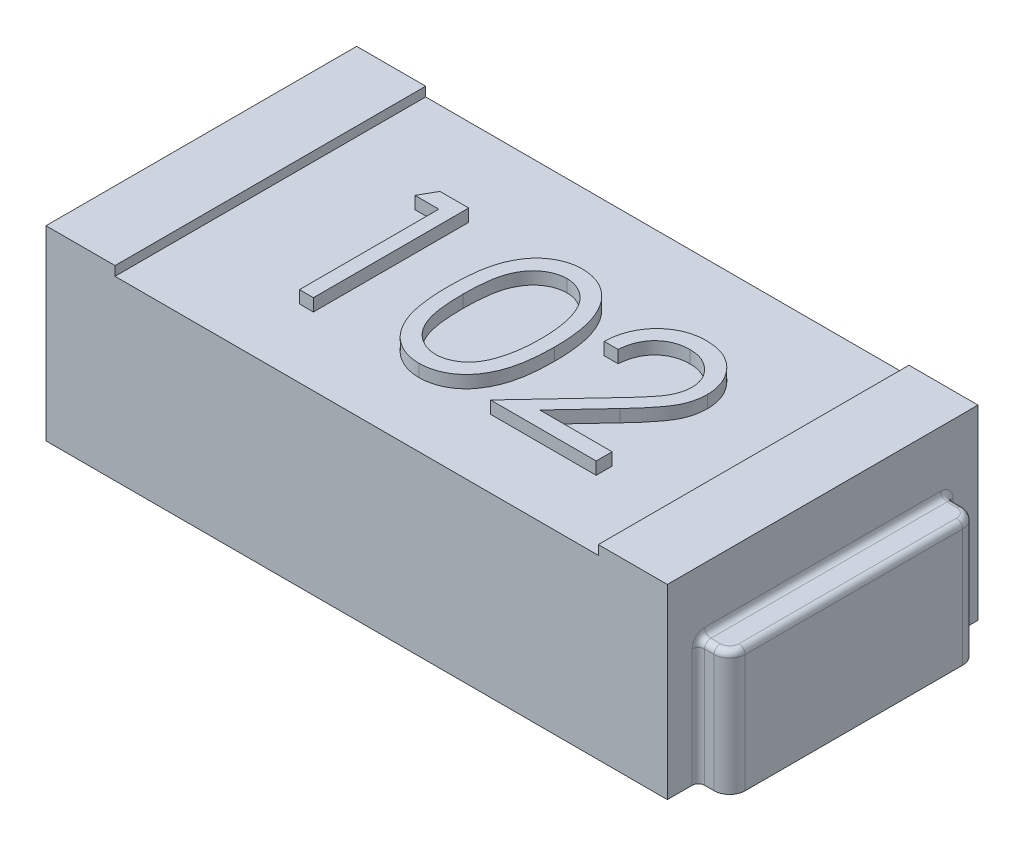
SolidWorks part; units mm, degrees
ref_plane "Plan de face" through (0, 0, 0) normal (0, 0, 1) x (1, 0, 0)
ref_plane "Plan de dessus" through (0, 0, 0) normal (0, 1, 0) x (1, 0, 0)
ref_plane "Plan de droite" through (0, 0, 0) normal (1, 0, 0) x (0, 0, -1)
sketch "Esquisse1" plane through (0, 0, 0) normal (0, 1, 0) x (1, 0, 0)
  line L1 (1, -0.5) -> (-1, -0.5)
  line L2 (1, -0.5) -> (1, 0.5)
  line L3 (1, 0.5) -> (-1, 0.5)
  line L4 (-1, -0.5) -> (-1, 0.5)
  line L5 (1, -0.5) -> (-1, 0.5) construction
  line L6 (1, 0.5) -> (-1, -0.5) construction
  point P0 (0, 0)
  dimension "D1" = 2
  dimension "D2" = 1
extrude "Boss.-Extru.1" add sketch "Esquisse1" along normal blind 0.6
sketch "Esquisse2" plane through (0, 0.6, 0) normal (0, 1, 0) x (1, 0, 0)
  line L0 (1, 0.5) -> (-1, 0.5) construction
  line L1 (0.7778, -0.5) -> (-0.7778, -0.5)
  line L2 (0.7778, -0.5) -> (0.7778, 0.5)
  line L3 (0.7778, 0.5) -> (-0.7778, 0.5)
  line L4 (-0.7778, -0.5) -> (-0.7778, 0.5)
  line L5 (0.7778, -0.5) -> (-0.7778, 0.5) construction
  line L6 (0.7778, 0.5) -> (-0.7778, -0.5) construction
  point P0 (0, 0)
extrude "Enlèv. mat.-Extru.1" cut sketch "Esquisse2" against normal blind 0.03
sketch "Esquisse3" plane through (0, 0, 0) normal (0, 1, 0) x (1, 0, 0)
  line L1 (1, 0.4) -> (1.0506, 0.4)
  line L2 (1, 0.4) -> (1, -0.4)
  line L3 (1, -0.4) -> (1.0506, -0.4)
  line L4 (1.1006, 0.35) -> (1.1006, -0.35)
  line L8 (1, -0.5) -> (1, 0.5) construction
  arc A0 (1.0506, -0.4) -> (1.1006, -0.35) centre (1.0506, -0.35) ccw
  arc A1 (1.0506, 0.4) -> (1.1006, 0.35) centre (1.0506, 0.35) cw
  dimension "D1" = 0.05
  dimension "D2" = 0.8
  dimension "D3" = 0.1006
extrude "Boss.-Extru.2" add sketch "Esquisse3" along normal blind 0.4
fillet "Congé1" radius 0.02 8 edges at (1, 0.2, -0.4) (1, 0.2, 0.4) (1.0253, 0.4, -0.4) (1.0859, 0.4, -0.3854) (1.1006, 0.4, 0) (1.0859, 0.4, 0.3854) (1.0253, 0.4, 0.4) (1, 0.4, 0)
mirror "Symétrie2" about plane through (0, 0, 0) normal (1, 0, 0) of "Congé1", "Boss.-Extru.2"
sketch "Esquisse4" plane through (0, 0.57, 0) normal (0, 1, 0) x (1, 0, 0)
  line L0 (0.7576, -0.2803) -> (-0.7576, -0.2803) construction
  text T0 "102\r\n" font "Century Gothic" height 0.5
  point P3 (0, -0.2803)
extrude "Boss.-Extru.3" add sketch "Esquisse4" along normal blind 0.04
